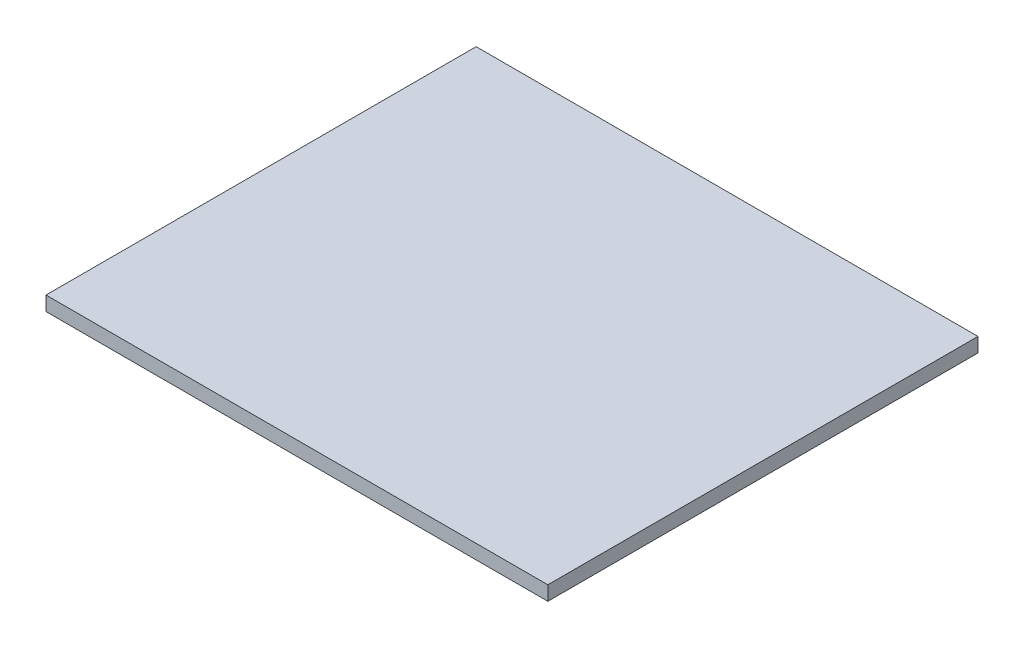
SolidWorks part; units mm, degrees
material "Плата системы питания"
ref_plane "Спереди" through (0, 0, 0) normal (0, 0, 1) x (1, 0, 0)
ref_plane "Сверху" through (0, 0, 0) normal (0, 1, 0) x (1, 0, 0)
ref_plane "Справа" through (0, 0, 0) normal (1, 0, 0) x (0, 0, -1)
sketch "Эскиз1" plane through (0, 0, 0) normal (0, 1, 0) x (1, 0, 0)
  line L1 (16.8935, 23.7593) -> (-39.1065, 23.7593)
  line L2 (16.8935, 23.7593) -> (16.8935, -24.2407)
  line L3 (16.8935, -24.2407) -> (-39.1065, -24.2407)
  line L4 (-39.1065, 23.7593) -> (-39.1065, -24.2407)
extrude "Бобышка-Вытянуть1" add sketch "Эскиз1" along normal blind 1.6 contours L1 L4 L3 L2
